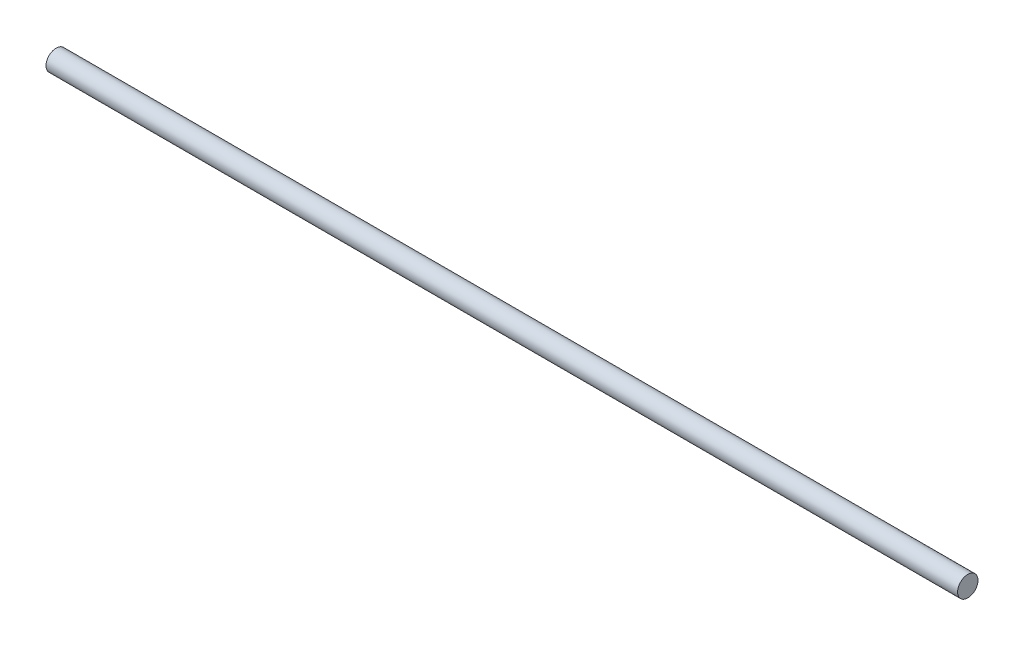
SolidWorks part; units mm, degrees
ref_plane "Front Plane" through (0, 0, 0) normal (0, 0, 1) x (1, 0, 0)
ref_plane "Top Plane" through (0, 0, 0) normal (0, 1, 0) x (1, 0, 0)
ref_plane "Right Plane" through (0, 0, 0) normal (1, 0, 0) x (0, 0, -1)
sketch "Sketch1" plane through (0, 0, 0) normal (0, 0, 1) x (1, 0, 0)
  line L0 (0, 0) -> (134, 0)
  line L1 (0, 0) -> (134, 0) construction
  line L2 (0, 0) -> (0, -1.5)
  line L3 (0, -1.5) -> (134, -1.5)
  line L4 (134, 0) -> (134, -1.5)
  dimension "D1" = 1.5
  dimension "D2" = 134
revolve "Revolve1" add sketch "Sketch1" angle 360 about L1
